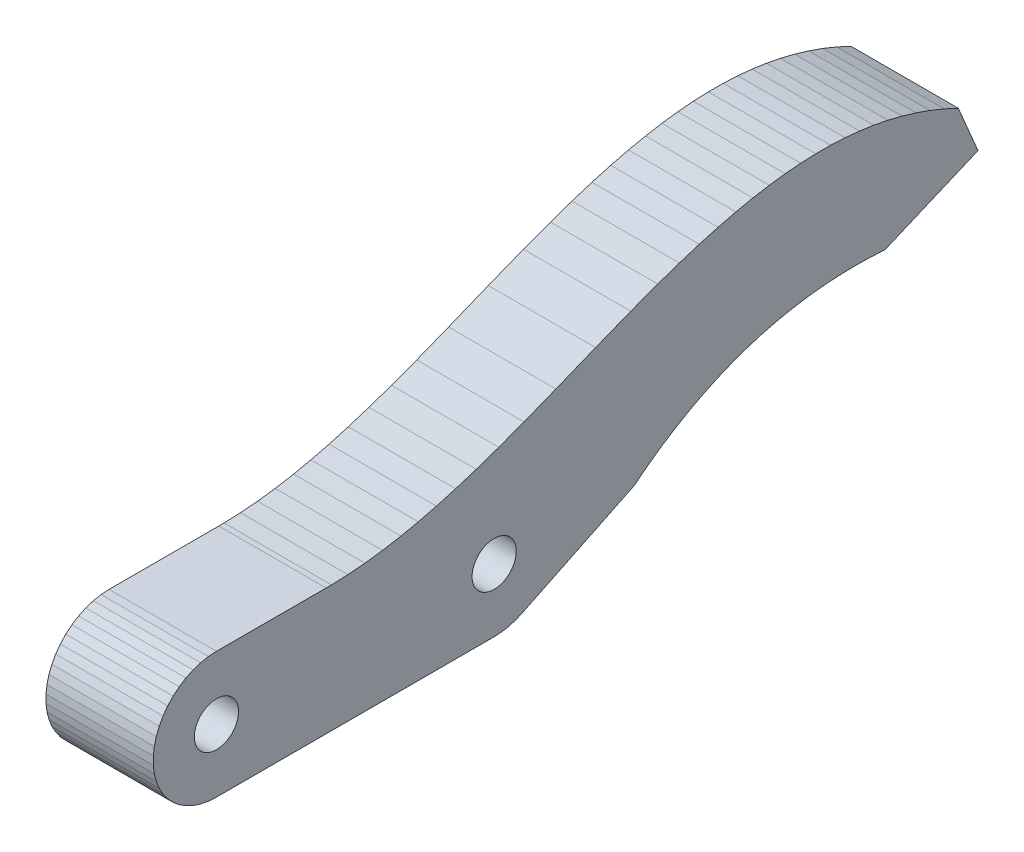
SolidWorks part; units mm, degrees
ref_plane "Front Plane" through (0, 0, 0) normal (0, 0, 1) x (1, 0, 0)
ref_plane "Top Plane" through (0, 0, 0) normal (0, 1, 0) x (1, 0, 0)
ref_plane "Right Plane" through (0, 0, 0) normal (1, 0, 0) x (0, 0, -1)
ref_plane "Plane1" through (0, 0, 0) normal (-1, 0, 0) x (0, -1, 0)
sketch "Sketch1" plane through (0, 0, 0) normal (-1, 0, 0) x (0, -1, 0)
  line L72 (-0.1271, 37.1934) -> (-0.0319, 37.75)
  line L73 (-0.0319, 37.75) -> (0, 38.3138)
  line L74 (0, 38.3138) -> (0, 60.3138)
  line L75 (0, 60.3138) -> (-0.0394, 60.9405)
  line L76 (-0.0394, 60.9405) -> (-0.1571, 61.5573)
  line L77 (-0.1571, 61.5573) -> (-0.3511, 62.1544)
  line L78 (-0.3511, 62.1544) -> (-0.6185, 62.7226)
  line L79 (-0.6185, 62.7226) -> (-0.9549, 63.2527)
  line L80 (-0.9549, 63.2527) -> (-1.3552, 63.7365)
  line L81 (-1.3552, 63.7365) -> (-1.8129, 64.1664)
  line L82 (-1.8129, 64.1664) -> (-2.3209, 64.5354)
  line L83 (-2.3209, 64.5354) -> (-2.8711, 64.8379)
  line L84 (-2.8711, 64.8379) -> (-3.4549, 65.0691)
  line L85 (-3.4549, 65.0691) -> (-4.0631, 65.2252)
  line L86 (-4.0631, 65.2252) -> (-4.686, 65.304)
  line L87 (-4.686, 65.304) -> (-5.314, 65.304)
  line L88 (-5.314, 65.304) -> (-5.9369, 65.2252)
  line L89 (-5.9369, 65.2252) -> (-6.5451, 65.0691)
  line L90 (-6.5451, 65.0691) -> (-7.1289, 64.8379)
  line L91 (-7.1289, 64.8379) -> (-7.6791, 64.5354)
  line L92 (-7.6791, 64.5354) -> (-8.1871, 64.1664)
  line L93 (-8.1871, 64.1664) -> (-8.6448, 63.7365)
  line L94 (-8.6448, 63.7365) -> (-9.0451, 63.2527)
  line L95 (-9.0451, 63.2527) -> (-9.3815, 62.7226)
  line L96 (-9.3815, 62.7226) -> (-9.6489, 62.1544)
  line L97 (-9.6489, 62.1544) -> (-9.8429, 61.5573)
  line L98 (-9.8429, 61.5573) -> (-9.9606, 60.9405)
  line L99 (-9.9606, 60.9405) -> (-10, 60.3138)
  line L100 (-10, 60.3138) -> (-10, 51.6188)
  line L101 (-10, 51.6188) -> (-10.0032, 51.2023)
  line L102 (-10.0032, 51.2023) -> (-10.0533, 49.8962)
  line L103 (-10.0533, 49.8962) -> (-10.1666, 48.5491)
  line L104 (-10.1666, 48.5491) -> (-10.3469, 47.1507)
  line L105 (-10.3469, 47.1507) -> (-10.599, 45.6906)
  line L106 (-10.599, 45.6906) -> (-10.8905, 44.3214)
  line L107 (-10.8905, 44.3214) -> (-11.2485, 42.8854)
  line L108 (-11.2485, 42.8854) -> (-11.6805, 41.3647)
  line L109 (-11.6805, 41.3647) -> (-12.1972, 39.7324)
  line L110 (-12.1972, 39.7324) -> (-12.8155, 37.9472)
  line L111 (-12.8155, 37.9472) -> (-13.5583, 35.9518)
  line L112 (-13.5583, 35.9518) -> (-14.5505, 33.4272)
  line L113 (-14.5505, 33.4272) -> (-15.8198, 30.2771)
  line L114 (-15.8198, 30.2771) -> (-16.9177, 27.4927)
  line L115 (-16.9177, 27.4927) -> (-17.7119, 25.3579)
  line L116 (-17.7119, 25.3579) -> (-18.3013, 23.6499)
  line L117 (-18.3013, 23.6499) -> (-18.7999, 22.069)
  line L118 (-18.7999, 22.069) -> (-19.2196, 20.584)
  line L119 (-19.2196, 20.584) -> (-19.568, 19.1744)
  line L120 (-19.568, 19.1744) -> (-19.8506, 17.8254)
  line L121 (-19.8506, 17.8254) -> (-20.0715, 16.5261)
  line L122 (-20.0715, 16.5261) -> (-20.2335, 15.2678)
  line L123 (-20.2335, 15.2678) -> (-20.3389, 14.0435)
  line L124 (-20.3389, 14.0435) -> (-20.3893, 12.8474)
  line L125 (-20.3893, 12.8474) -> (-20.3855, 11.6745)
  line L126 (-20.3855, 11.6745) -> (-20.3283, 10.5204)
  line L127 (-20.3283, 10.5204) -> (-20.2176, 9.3812)
  line L128 (-20.2176, 9.3812) -> (-20.0532, 8.2535)
  line L129 (-20.0532, 8.2535) -> (-19.8344, 7.134)
  line L130 (-19.8344, 7.134) -> (-19.5601, 6.0199)
  line L131 (-19.5601, 6.0199) -> (-19.2289, 4.9083)
  line L132 (-19.2289, 4.9083) -> (-18.839, 3.7967)
  line L133 (-18.839, 3.7967) -> (-18.3882, 2.6828)
  line L134 (-18.3882, 2.6828) -> (-17.8724, 1.5608)
  line L135 (-17.8724, 1.5608) -> (-14.1895, 0)
  line L136 (-14.1895, 0) -> (-11.0678, 7.3658)
  line L137 (-11.0678, 7.3658) -> (-11.1299, 8.4504)
  line L138 (-11.1299, 8.4504) -> (-11.1544, 9.7625)
  line L139 (-11.1544, 9.7625) -> (-11.1226, 11.0498)
  line L140 (-11.1226, 11.0498) -> (-11.0354, 12.3138)
  line L141 (-11.0354, 12.3138) -> (-10.8934, 13.5561)
  line L142 (-10.8934, 13.5561) -> (-10.697, 14.778)
  line L143 (-10.697, 14.778) -> (-10.4463, 15.9812)
  line L144 (-10.4463, 15.9812) -> (-10.1413, 17.1668)
  line L145 (-10.1413, 17.1668) -> (-9.7815, 18.3362)
  line L146 (-9.7815, 18.3362) -> (-9.3665, 19.4906)
  line L147 (-9.3665, 19.4906) -> (-8.8954, 20.6312)
  line L148 (-8.8954, 20.6312) -> (-8.3672, 21.7589)
  line L149 (-8.3672, 21.7589) -> (-7.7807, 22.8748)
  line L150 (-7.7807, 22.8748) -> (-7.1343, 23.9797)
  line L151 (-7.1343, 23.9797) -> (-6.4264, 25.0745)
  line L152 (-6.4264, 25.0745) -> (-5.655, 26.1596)
  line L153 (-5.655, 26.1596) -> (-4.8241, 27.2284)
  line L154 (-4.8241, 27.2284) -> (-0.5021, 36.13)
  line L155 (-0.5021, 36.13) -> (-0.2846, 36.6511)
  line L156 (-0.2846, 36.6511) -> (-0.1271, 37.1934)
  circle A0 centre (-5.0012, 60.3072) radius 1.75
  circle A2 centre (-5, 38.3138) radius 1.75
extrude "Boss-Extrude1" add sketch "Sketch1" against normal blind 8.5
